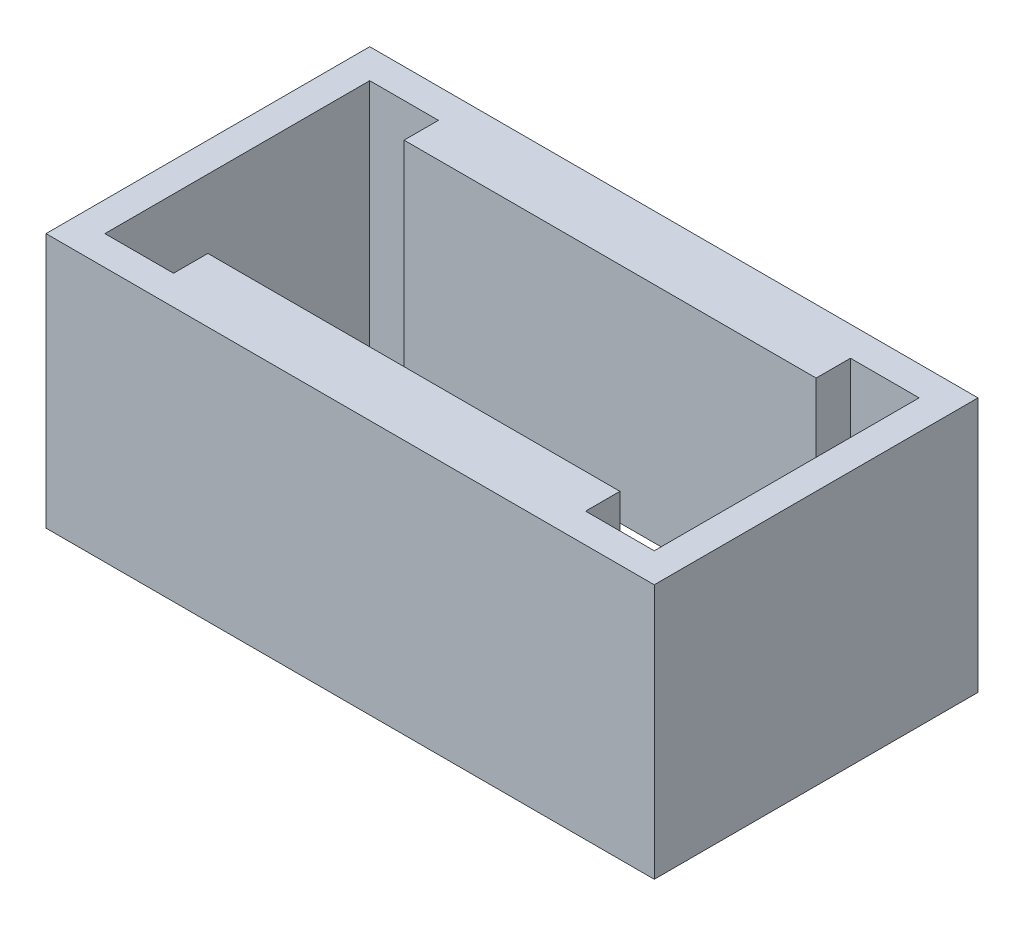
SolidWorks part; units mm, degrees
ref_plane "Front Plane" through (0, 0, 0) normal (0, 0, 1) x (1, 0, 0)
ref_plane "Top Plane" through (0, 0, 0) normal (0, 1, 0) x (1, 0, 0)
ref_plane "Right Plane" through (0, 0, 0) normal (1, 0, 0) x (0, 0, -1)
sketch "Sketch1" plane through (0, 0, 0) normal (0, 1, 0) x (1, 0, 0)
  line L0 (0, 0) -> (-14, 0) construction
  line L1 (10.5, 5) -> (-10.5, 5)
  line L2 (10.5, 5) -> (10.5, -5) construction
  line L3 (10.5, -5) -> (-10.5, -5)
  line L4 (-10.5, 6.75) -> (-10.5, 5)
  line L5 (10.5, 5) -> (-10.5, -5) construction
  line L6 (10.5, -5) -> (-10.5, 5) construction
  line L7 (-10.5, -6.75) -> (-14, -6.75)
  line L8 (-10.5, -6.75) -> (-10.5, -5)
  line L9 (-10.5, 6.75) -> (-14, 6.75)
  line L10 (-14, -6.75) -> (-14, 6.75)
  line L12 (15.5, -8.25) -> (-15.5, -8.25)
  line L13 (-10.5, 5) -> (-10.5, -5) construction
  line L14 (0, 0) -> (14, 0) construction
  line L15 (10.5, -6.75) -> (14, -6.75)
  line L16 (10.5, 6.75) -> (10.5, 5)
  line L17 (10.5, 6.75) -> (14, 6.75)
  line L18 (14, -6.75) -> (14, 6.75)
  line L19 (10.5, -5) -> (10.5, -6.75)
  line L20 (15.5, -8.25) -> (15.5, 8.25)
  line L21 (15.5, 8.25) -> (-15.5, 8.25)
  line L22 (-15.5, -8.25) -> (-15.5, 8.25)
  line L23 (15.5, -8.25) -> (-15.5, 8.25) construction
  line L24 (15.5, 8.25) -> (-15.5, -8.25) construction
  point P0 (0, 0)
  dimension "D1" = 10
  dimension "D2" = 21
  dimension "D4" = 13.5
  dimension "D5" = 13.5
  dimension "D6" = 3.5
  dimension "D7" = 1.5
  dimension "D8" = 16.5
extrude "Boss-Extrude1" add sketch "Sketch1" along normal blind 13
sketch "Sketch2" plane through (0, 0, 0) normal (0, -1, 0) x (1, 0, 0)
  line L1 (10.5, 6.75) -> (-10.5, 6.75)
  line L2 (10.5, 6.75) -> (10.5, 5)
  line L3 (10.5, 5) -> (-10.5, 5)
  line L4 (-10.5, 6.75) -> (-10.5, 5)
  line L5 (10.5, 6.75) -> (-10.5, 5) construction
  line L6 (10.5, 5) -> (-10.5, 6.75) construction
  line L7 (10.5, -6.75) -> (-10.5, -6.75)
  line L8 (10.5, -6.75) -> (10.5, -5)
  line L9 (10.5, -5) -> (-10.5, -5)
  line L10 (-10.5, -6.75) -> (-10.5, -5)
  line L11 (10.5, -6.75) -> (-10.5, -5) construction
  line L12 (10.5, -5) -> (-10.5, -6.75) construction
  point P0 (0, 5.875)
  point P6 (0, -5.875)
extrude "Cut-Extrude1" cut sketch "Sketch2" against normal blind 1.6
